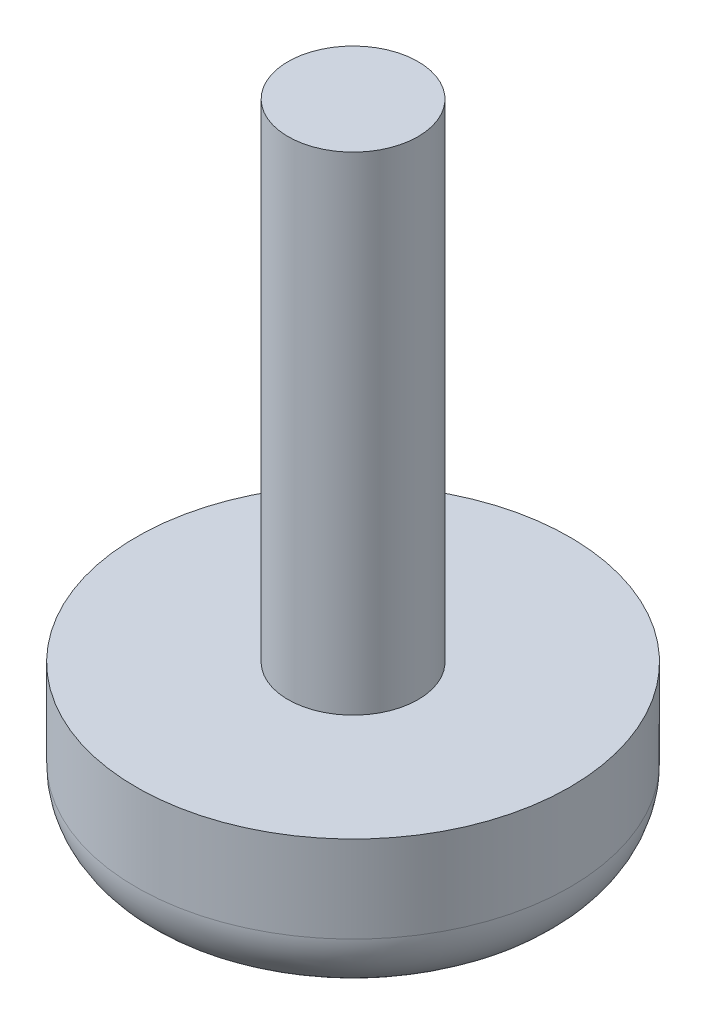
SolidWorks part; units mm, degrees
ref_plane "Plan de face" through (0, 0, 0) normal (0, 0, 1) x (1, 0, 0)
ref_plane "Plan de dessus" through (0, 0, 0) normal (0, 1, 0) x (1, 0, 0)
ref_plane "Plan de droite" through (0, 0, 0) normal (1, 0, 0) x (0, 0, -1)
sketch "Esquisse1" plane through (0, 0, 0) normal (0, 0, 1) x (1, 0, 0)
  line L1 (0, 0) -> (-3, 0)
  line L2 (0, 0) -> (0, 22.5)
  line L3 (0, 22.5) -> (-3, 22.5)
  line L4 (-3, 0) -> (-3, 22.5)
  line L5 (0, 0) -> (-10, 0)
  line L6 (0, 0) -> (0, -7)
  line L7 (0, -7) -> (-10, -7)
  line L8 (-10, 0) -> (-10, -7)
  dimension "D1" = 3
  dimension "D2" = 7
  dimension "D3" = 22.5
  dimension "D4" = 10
revolve "Révolution1" add sketch "Esquisse1" angle 360 about L2
fillet "Congé1" radius 3 1 edges at (10, -7, 0)
